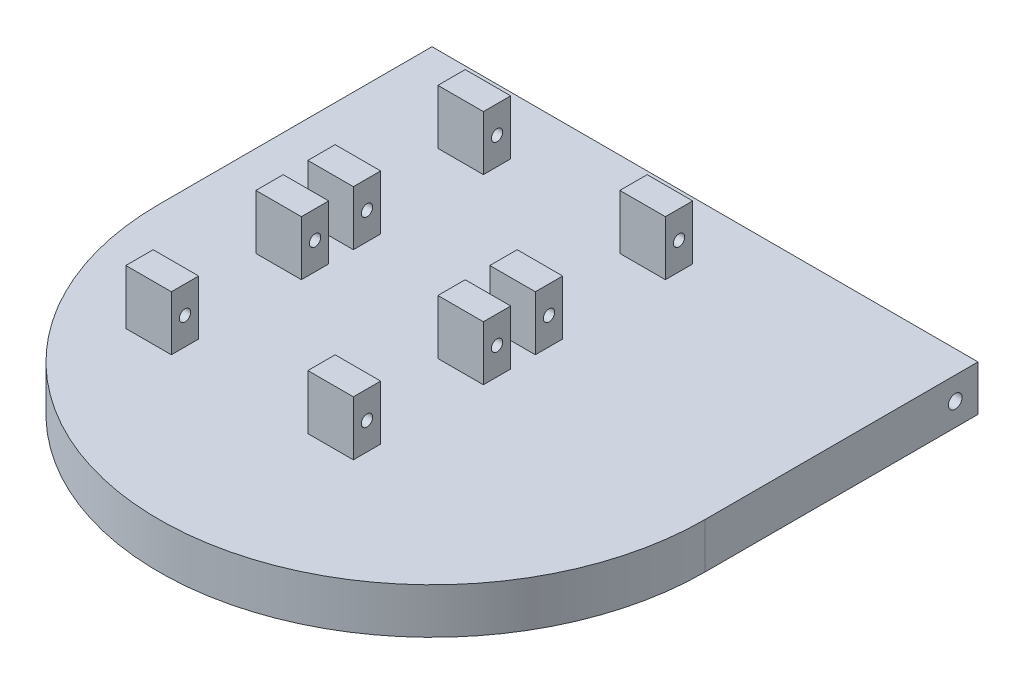
SolidWorks part; units mm, degrees
ref_plane "Front Plane" through (0, 0, 0) normal (0, 0, 1) x (1, 0, 0)
ref_plane "Top Plane" through (0, 0, 0) normal (0, 1, 0) x (1, 0, 0)
ref_plane "Right Plane" through (0, 0, 0) normal (1, 0, 0) x (0, 0, -1)
sketch "Sketch1" plane through (0, 0, 0) normal (0, 1, 0) x (1, 0, 0)
  line L0 (-60, 0) -> (-60, 60)
  line L1 (-60, 60) -> (60, 60)
  line L2 (60, 60) -> (60, 0)
  arc A0 (-60, 0) -> (60, 0) centre (0, 0) ccw
  dimension "D1" = 120
  dimension "D2" = 120
extrude "Boss-Extrude1" add sketch "Sketch1" along normal blind 10
sketch "Sketch2" plane through (-60, 0, 0) normal (-1, 0, 0) x (0, 0, 1)
  line L0 (-60, 0) -> (0, 0) construction
  line L1 (-60, 10) -> (-60, 0) construction
  circle A0 centre (-55, 5) radius 1.5
  dimension "D1" = 3
  dimension "D2" = 5
  dimension "D3" = 5
extrude "Cut-Extrude1" cut sketch "Sketch2" against normal through all both and the other way through all
sketch "Sketch5" plane through (-60, 0, 0) normal (-1, 0, 0) x (0, 0, 1)
  line L0 (-60, 10) -> (0, 10) construction
  line L1 (-47.29, 10) -> (-41.29, 10)
  line L2 (-47.29, 10) -> (-47.29, 22)
  line L3 (-47.29, 22) -> (-41.29, 22)
  line L4 (-41.29, 10) -> (-41.29, 22)
  line L5 (-44.29, 16) -> (-15.71, 16) construction
  line L6 (-18.71, 10) -> (-12.71, 10)
  line L7 (-18.71, 10) -> (-18.71, 22)
  line L8 (-18.71, 22) -> (-12.71, 22)
  line L9 (-12.71, 10) -> (-12.71, 22)
  line L10 (-30, 16) -> (-30, 10) construction
  line L11 (-41.29, 22) -> (-18.71, 22) construction
  line L12 (-60, 10) -> (-60, 0) construction
  line L13 (-44.29, 16) -> (-44.29, 22) construction
  circle A0 centre (-44.29, 16) radius 1.25
  circle A1 centre (-15.71, 16) radius 1.25
  point P17 (-30, 22)
  dimension "D1" = 2.5
  dimension "D2" = 12
  dimension "D3" = 6
  dimension "D4" = 28.58
  dimension "D5" = 6
  dimension "D6" = 30
extrude "Boss-Extrude2" add sketch "Sketch5" against normal blind 10 from offset 20 offset against normal yes
pattern_linear "LPattern1" count 2 spacing 40 along (1, 0, 0) count 2 spacing 40 along (0, 0, 1) of "Boss-Extrude2"
sketch "Sketch6" plane through (0, 10, 0) normal (0, 1, 0) x (1, 0, 0)
  line L0 (-42.4264, -42.4264) -> (-14.1421, -14.1421)
  line L1 (-42.4264, -42.4264) -> (-120.2082, 35.3553)
  line L2 (-14.1421, -14.1421) -> (-91.9239, 63.6396)
  line L3 (-120.2082, 35.3553) -> (-91.9239, 63.6396)
  line L4 (0, 0) -> (-14.1421, -14.1421) construction
  line L5 (60, 60) -> (-60, 60) construction
  arc A0 (-60, 0) -> (60, 0) centre (0, 0) ccw construction
  dimension "D1" = 110
  dimension "D2" = 40
  dimension "D3" = 45
extrude "Boss-Extrude3" [suppressed] add sketch "Sketch6" against normal blind 50
sketch "Sketch8" [suppressed] plane through (-77.7817, 0, -77.7817) normal (-0.7071, 0, -0.7071) x (-0.7071, 0, 0.7071)
  line L1 (20, -40) -> (20, 10) construction
  line L2 (20, -40) -> (60, -40) construction
  circle A0 centre (25, -35) radius 1.5
  dimension "D1" = 3
  dimension "D2" = 5
  dimension "D3" = 5
extrude "Cut-Extrude2" [suppressed] cut sketch "Sketch8" against normal blind 10
sketch "Sketch9" plane through (0, 0, 0) normal (0, -1, 0) x (1, 0, 0)
  line L0 (-53.5483, -27.0128) -> (-43.4437, -21.1789)
  line L1 (-53.5483, -27.0128) -> (-51.944, -29.7915)
  line L2 (-43.4437, -21.1789) -> (-41.8394, -23.9576)
  line L3 (-51.944, -29.7915) -> (-41.8394, -23.9576)
  line L4 (-53.5483, -27.0128) -> (-41.8394, -23.9576) construction
  line L5 (-43.4437, -21.1789) -> (-51.944, -29.7915) construction
  line L6 (-60, -60) -> (-60, 0) construction
  line L7 (-9.9576, -1.8457) -> (0.147, 3.9882)
  line L8 (-9.9576, -1.8457) -> (-8.3533, -4.6243)
  line L9 (0.147, 3.9882) -> (1.7513, 1.2095)
  line L10 (-8.3533, -4.6243) -> (1.7513, 1.2095)
  line L11 (-9.9576, -1.8457) -> (1.7513, 1.2095) construction
  line L12 (0.147, 3.9882) -> (-8.3533, -4.6243) construction
  point P1 (-47.6939, -25.4852)
  point P8 (-4.1031, -0.3181)
  dimension "D1" = 30
  dimension "D2" = 38.6665
extrude "Boss-Extrude4" add sketch "Sketch9" along normal blind 18
chamfer "Chamfer1" distance 15 angle 45 2 edges at (-3.301, 0, -1.7074) (-46.8917, 0, -26.8745)
